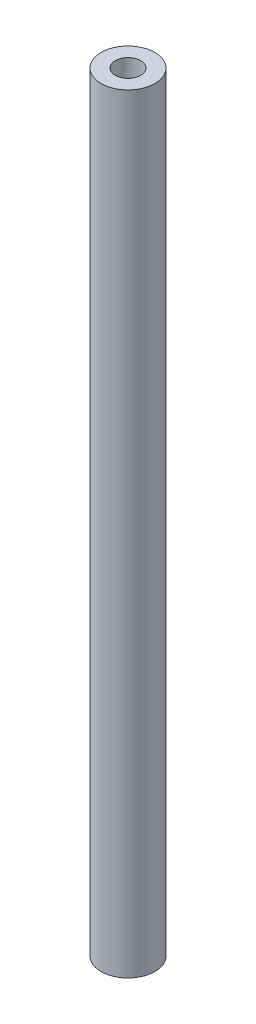
SolidWorks part; units mm, degrees
material "ABS"
ref_plane "Front Plane" through (0, 0, 0) normal (0, 0, 1) x (1, 0, 0)
ref_plane "Top Plane" through (0, 0, 0) normal (0, 1, 0) x (1, 0, 0)
ref_plane "Right Plane" through (0, 0, 0) normal (1, 0, 0) x (0, 0, -1)
sketch "Sketch1" plane through (0, 0, 0) normal (0, 1, 0) x (1, 0, 0)
  circle A0 centre (0, 0) radius 4.9638
  circle A1 centre (0, 0) radius 10.5
  dimension "D1" = 21
extrude "Boss-Extrude1" add sketch "Sketch1" along normal blind 300
